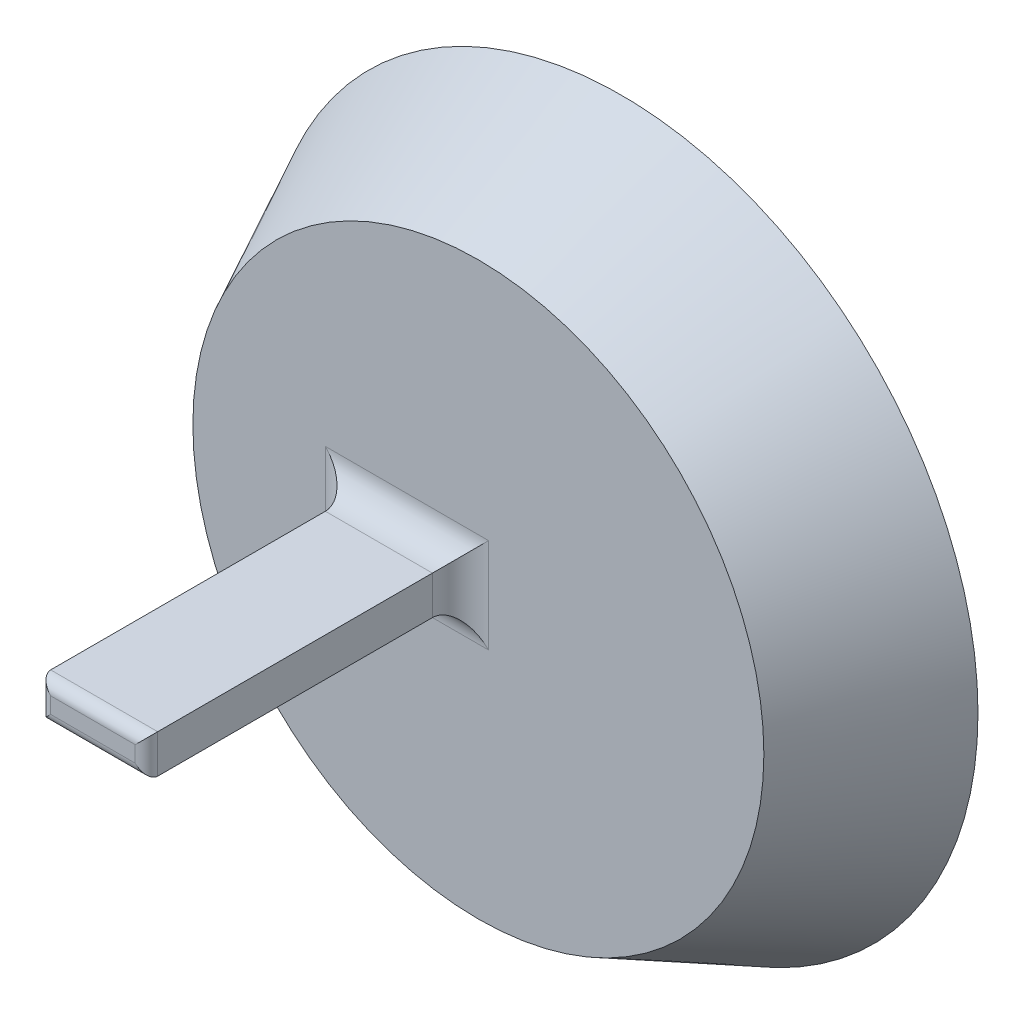
SolidWorks part; units mm, degrees
ref_plane "Front Plane" through (0, 0, 0) normal (0, 0, 1) x (1, 0, 0)
ref_plane "Top Plane" through (0, 0, 0) normal (0, 1, 0) x (1, 0, 0)
ref_plane "Right Plane" through (0, 0, 0) normal (1, 0, 0) x (0, 0, -1)
sketch "Sketch1" plane through (0, 0, 0) normal (0, 0, 1) x (1, 0, 0)
  circle A0 centre (0, 0) radius 63.5
  dimension "D1" = 127
ref_plane "Plane1" through (0, 0, 25.4) normal (0, 0, 1) x (1, 0, 0)
sketch "Sketch2" plane through (0, 0, 25.4) normal (0, 0, 1) x (1, 0, 0)
  circle A0 centre (0, 0) radius 50.8
  dimension "D1" = 101.6
loft "Loft1" add profiles "Sketch1", "Sketch2"
shell "Shell1" thickness 10
sketch "Sketch3" plane through (0, 0, 25.4) normal (0, 0, 1) x (1, 0, 0)
  line L1 (-3.175, -3.429) -> (-22.225, -3.429)
  line L2 (-3.175, -3.429) -> (-3.175, 3.429)
  line L3 (-3.175, 3.429) -> (-22.225, 3.429)
  line L4 (-22.225, -3.429) -> (-22.225, 3.429)
  line L5 (-3.175, -3.429) -> (-22.225, 3.429) construction
  line L6 (-3.175, 3.429) -> (-22.225, -3.429) construction
  point P0 (0, 0)
  point P8 (-12.7, 0)
  dimension "D1" = 6.858
  dimension "D2" = 19.05
  dimension "D3" = 12.7
extrude "Boss-Extrude1" add sketch "Sketch3" along normal blind 55.88
fillet "Fillet2" radius 2 4 edges at (-12.7, 3.429, 81.28) (-3.175, 0, 81.28) (-12.7, -3.429, 81.28) (-22.225, 0, 81.28)
fillet "Fillet3" radius 5 4 edges at (-22.225, 0, 25.4) (-12.7, 3.429, 25.4) (-3.175, 0, 25.4) (-12.7, -3.429, 25.4)
